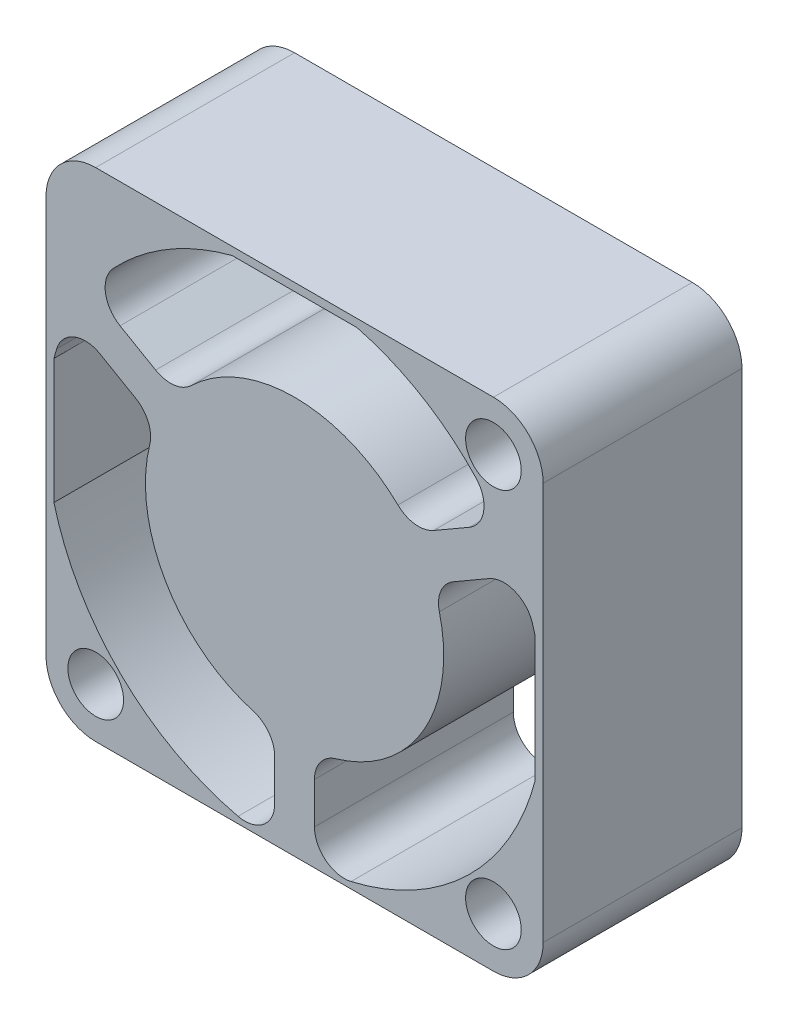
SolidWorks part; units mm, degrees
ref_plane "Front Plane" through (0, 0, 0) normal (0, 0, 1) x (1, 0, 0)
ref_plane "Top Plane" through (0, 0, 0) normal (0, 1, 0) x (1, 0, 0)
ref_plane "Right Plane" through (0, 0, 0) normal (1, 0, 0) x (0, 0, -1)
sketch "Sketch1" plane through (0, 0, 0) normal (0, 0, 1) x (1, 0, 0)
  line L1 (-12.5, 12.5) -> (12.5, 12.5)
  line L2 (-12.5, 12.5) -> (-12.5, -12.5)
  line L3 (-12.5, -12.5) -> (12.5, -12.5)
  line L4 (12.5, 12.5) -> (12.5, -12.5)
  line L5 (-12.5, 12.5) -> (12.5, -12.5) construction
  line L6 (-12.5, -12.5) -> (12.5, 12.5) construction
  point P0 (0, 0)
  dimension "D1" = 25
  dimension "D2" = 25
extrude "Extrude1" add sketch "Sketch1" along normal blind 10
fillet "Fillet1" radius 2.5 4 edges at (12.5, -12.5, 5) (-12.5, -12.5, 5) (-12.5, 12.5, 5) (12.5, 12.5, 5)
sketch "Sketch2" plane through (0, 0, 10) normal (0, 0, 1) x (1, 0, 0)
  line L0 (-3.1369, 12.1) -> (3.1369, 12.1)
  line L1 (12.1, 3.1369) -> (12.1, -3.1369)
  line L3 (-12.1, 3.1369) -> (-12.1, -3.1369)
  line L4 (10, 12.5) -> (-10, 12.5) construction
  line L5 (12.5, -10) -> (12.5, 10) construction
  line L7 (-12.5, 10) -> (-12.5, -10) construction
  line L8 (0, 0) -> (11.9499, 6.8993) construction
  line L9 (0, 0) -> (0, -15.5024) construction
  line L10 (0, 0) -> (-15.6943, 9.0611) construction
  line L11 (5.9372, 4.5825) -> (10.2906, 7.096)
  line L12 (6.9372, 2.8505) -> (11.2906, 5.3639)
  line L13 (-1, -12.4599) -> (-1, -7.433)
  line L14 (1, -12.4599) -> (1, -7.433)
  line L15 (-6.9372, 2.8505) -> (-11.2906, 5.3639)
  line L16 (-5.9372, 4.5825) -> (-10.2906, 7.096)
  arc A0 (5.9372, 4.5825) -> (-5.9372, 4.5825) centre (0, 0) ccw
  arc A1 (-3.1369, 12.1) -> (-10.2906, 7.096) centre (0, 0) ccw
  arc A2 (10.2906, 7.096) -> (3.1369, 12.1) centre (0, 0) ccw
  arc A3 (12.1, 3.1369) -> (11.2906, 5.3639) centre (0, 0) ccw
  arc A4 (1, -7.433) -> (6.9372, 2.8505) centre (0, 0) ccw
  arc A5 (1, -12.4599) -> (12.1, -3.1369) centre (0, 0) ccw
  arc A6 (-12.1, -3.1369) -> (-1, -12.4599) centre (0, 0) ccw
  arc A7 (-11.2906, 5.3639) -> (-12.1, 3.1369) centre (0, 0) ccw
  arc A8 (-6.9372, 2.8505) -> (-1, -7.433) centre (0, 0) ccw
  dimension "D1" = 15
  dimension "D2" = 25
  dimension "D9" = 2
  dimension "D3" = 0.4
  dimension "D4" = 0.4
  dimension "D6" = 0.4
  dimension "D7" = 120
  dimension "D8" = 120
  dimension "D10" = 1
  dimension "D11" = 2
  dimension "D12" = 1
  dimension "D13" = 2
  dimension "D14" = 1
extrude "Extrude2" cut sketch "Sketch2" against normal up to next
fillet "Fillet2" radius 1.5 12 edges at (-1, -7.433, 5) (-1, -12.4599, 5) (1, -12.4599, 5) (1, -7.433, 5) (6.9372, 2.8505, 5) (11.2906, 5.3639, 5) (10.2906, 7.096, 5) (5.9372, 4.5825, 5) (-10.2906, 7.096, 5) (-11.2906, 5.3639, 5) (-5.9372, 4.5825, 5) (-6.9372, 2.8505, 5)
hole_wizard "Ø2.8 (2.8) Diameter Hole1" positions "Sketch4" profile "Sketch3" hole size "Ø2.8" standard "ISO" end condition up to next
sketch "Sketch4" plane through (0, 0, 10) normal (0, 0, 1) x (1, 0, 0)
  point P0 (10, 10)
  point P1 (10, -10)
  point P3 (-10, -10)
  dimension "D1" = 10
  dimension "D2" = 20
  dimension "D3" = 20
  dimension "D4" = 10
sketch "Sketch3" plane through (10, 10, 10) normal (1, 0, 0) x (0, -1, 0)
  line L0 (0, 0) -> (0, 10)
  line L1 (0, 10) -> (1.4, 10)
  line L2 (1.4, 10) -> (1.4, 0)
  line L5 (1.4, 0) -> (0, 0)
  line L11 (0, -6.35) -> (0, 107.95) construction
  dimension "Thru Hole Dia." = 2.8
  dimension "Thru Hole Depth" = 10
